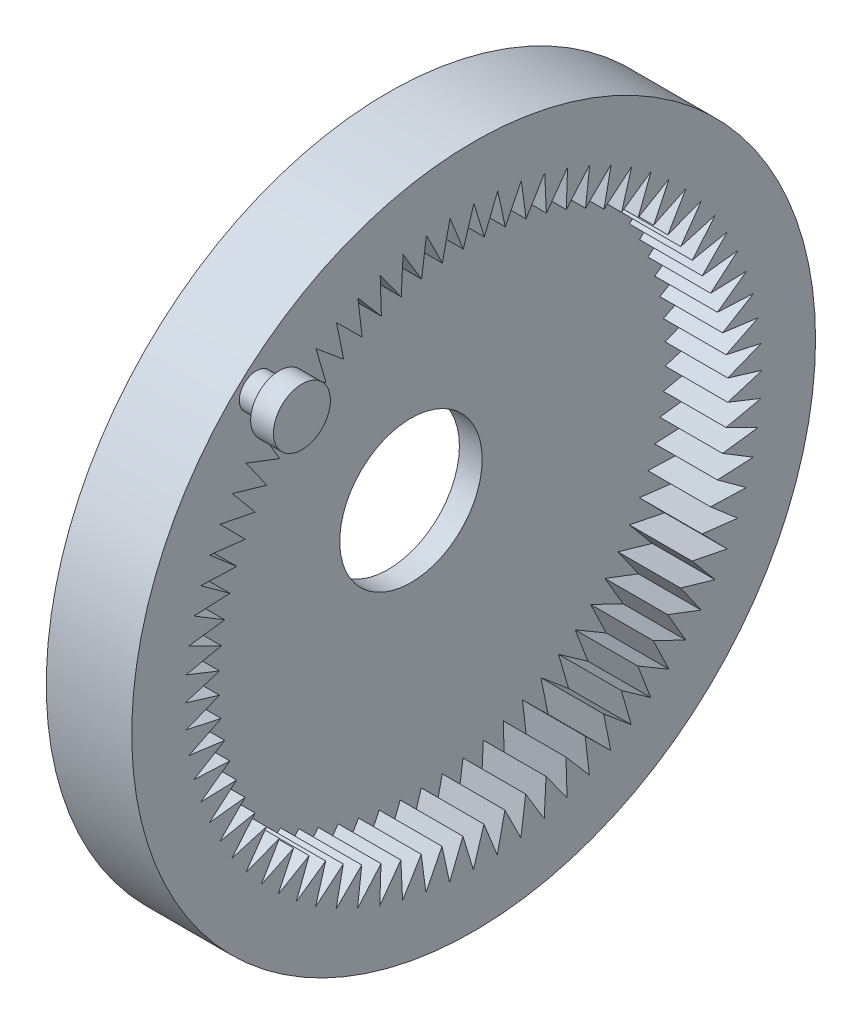
SolidWorks part; units mm, degrees
ref_plane "Front Plane" through (0, 0, 0) normal (0, 0, 1) x (1, 0, 0)
ref_plane "Top Plane" through (0, 0, 0) normal (0, 1, 0) x (1, 0, 0)
ref_plane "Right Plane" through (0, 0, 0) normal (1, 0, 0) x (0, 0, -1)
sketch "Sketch1" plane through (0, 0, 0) normal (1, 0, 0) x (0, 0, -1)
  circle A0 centre (0, 0) radius 30
  dimension "D1" = 60
extrude "Boss-Extrude1" add sketch "Sketch1" along normal blind 7.5
sketch "Sketch4" plane through (7.5, 0, 0) normal (1, 0, 0) x (0, -1, 0)
  line L0 (8.2003, -23.949) -> (8.0956, -20.7964)
  line L1 (8.2003, -23.949) -> (7.2077, -21.0502) construction
  line L2 (8.2003, -23.949) -> (6.3506, -21.3939)
  line L3 (6.1946, -24.5444) -> (6.3506, -21.3939)
  line L5 (6.1946, -24.5444) -> (4.5623, -21.8453)
  line L6 (4.1466, -24.9721) -> (4.5623, -21.8453)
  line L7 (4.1466, -24.9721) -> (2.7427, -22.1474)
  line L8 (2.0703, -25.2292) -> (2.7427, -22.1474)
  line L9 (2.0703, -25.2292) -> (0.9044, -22.2983)
  line L10 (-0.0202, -25.314) -> (0.9044, -22.2983)
  line L11 (-0.0202, -25.314) -> (-0.9401, -22.2968)
  line L12 (-2.1106, -25.2259) -> (-0.9401, -22.2968)
  line L13 (-2.1106, -25.2259) -> (-2.7781, -22.143)
  line L14 (-4.1865, -24.9654) -> (-2.7781, -22.143)
  line L15 (-4.1865, -24.9654) -> (-4.5972, -21.838)
  line L16 (-6.2338, -24.5345) -> (-4.5972, -21.838)
  line L17 (-6.2338, -24.5345) -> (-6.3848, -21.3837)
  line L18 (-8.2386, -23.9359) -> (-6.3848, -21.3837)
  line L19 (-8.2386, -23.9359) -> (-8.1289, -20.7835)
  line L20 (-10.1871, -23.1738) -> (-8.1289, -20.7835)
  line L21 (-10.1871, -23.1738) -> (-9.8174, -20.0412)
  line L22 (-12.0659, -22.2534) -> (-9.8174, -20.0412)
  line L23 (-12.0659, -22.2534) -> (-11.4389, -19.162)
  line L24 (-13.8624, -21.181) -> (-11.4389, -19.162)
  line L25 (-13.8624, -21.181) -> (-12.9822, -18.152)
  line L26 (-15.5642, -19.9639) -> (-12.9822, -18.152)
  line L27 (-15.5642, -19.9639) -> (-14.4368, -17.0179)
  line L28 (-17.1596, -18.6104) -> (-14.4368, -17.0179)
  line L29 (-17.1596, -18.6104) -> (-15.7928, -15.7676)
  line L30 (-18.6378, -17.1298) -> (-15.7928, -15.7676)
  line L31 (-18.6378, -17.1298) -> (-17.041, -14.4096)
  line L32 (-19.9887, -15.5322) -> (-17.041, -14.4096)
  line L33 (-19.9887, -15.5322) -> (-18.1727, -12.9531)
  line L34 (-21.2031, -13.8285) -> (-18.1727, -12.9531)
  line L35 (-21.2031, -13.8285) -> (-19.1803, -11.4082)
  line L36 (-22.2726, -12.0304) -> (-19.1803, -11.4082)
  line L37 (-22.2726, -12.0304) -> (-20.0569, -9.7854)
  line L38 (-23.19, -10.15) -> (-20.0569, -9.7854)
  line L39 (-23.19, -10.15) -> (-20.7964, -8.0956)
  line L40 (-23.949, -8.2003) -> (-20.7964, -8.0956)
  line L41 (-23.949, -8.2003) -> (-21.3939, -6.3506)
  line L42 (-24.5444, -6.1946) -> (-21.3939, -6.3506)
  line L43 (-24.5444, -6.1946) -> (-21.8453, -4.5623)
  line L44 (-24.9721, -4.1466) -> (-21.8453, -4.5623)
  line L45 (-24.9721, -4.1466) -> (-22.1474, -2.7427)
  line L46 (-25.2292, -2.0703) -> (-22.1474, -2.7427)
  line L47 (-25.2292, -2.0703) -> (-22.2983, -0.9044)
  line L48 (-25.314, 0.0202) -> (-22.2983, -0.9044)
  line L49 (-25.314, 0.0202) -> (-22.2968, 0.9401)
  line L50 (-25.2259, 2.1106) -> (-22.2968, 0.9401)
  line L51 (-25.2259, 2.1106) -> (-22.143, 2.7781)
  line L52 (-24.9654, 4.1865) -> (-22.143, 2.7781)
  line L53 (-24.9654, 4.1865) -> (-21.838, 4.5972)
  line L54 (-24.5345, 6.2338) -> (-21.838, 4.5972)
  line L55 (-24.5345, 6.2338) -> (-21.3837, 6.3848)
  line L56 (-23.9359, 8.2386) -> (-21.3837, 6.3848)
  line L57 (-23.9359, 8.2386) -> (-20.7835, 8.1289)
  line L58 (-23.1738, 10.1871) -> (-20.7835, 8.1289)
  line L59 (-23.1738, 10.1871) -> (-20.0412, 9.8174)
  line L60 (-22.2534, 12.0659) -> (-20.0412, 9.8174)
  line L61 (-22.2534, 12.0659) -> (-19.162, 11.4389)
  line L62 (-21.181, 13.8624) -> (-19.162, 11.4389)
  line L63 (-21.181, 13.8624) -> (-18.152, 12.9822)
  line L64 (-19.9639, 15.5642) -> (-18.152, 12.9822)
  line L65 (-19.9639, 15.5642) -> (-17.0179, 14.4368)
  line L66 (-18.6104, 17.1596) -> (-17.0179, 14.4368)
  line L67 (-18.6104, 17.1596) -> (-15.7676, 15.7928)
  line L68 (-17.1298, 18.6378) -> (-15.7676, 15.7928)
  line L69 (-17.1298, 18.6378) -> (-14.4096, 17.041)
  line L70 (-15.5322, 19.9887) -> (-14.4096, 17.041)
  line L71 (-15.5322, 19.9887) -> (-12.9531, 18.1727)
  line L72 (-13.8285, 21.2031) -> (-12.9531, 18.1727)
  line L73 (-13.8285, 21.2031) -> (-11.4082, 19.1803)
  line L74 (-12.0304, 22.2726) -> (-11.4082, 19.1803)
  line L75 (-12.0304, 22.2726) -> (-9.7854, 20.0569)
  line L76 (-10.15, 23.19) -> (-9.7854, 20.0569)
  line L77 (-10.15, 23.19) -> (-8.0956, 20.7964)
  line L78 (-8.2003, 23.949) -> (-8.0956, 20.7964)
  line L79 (-8.2003, 23.949) -> (-6.3506, 21.3939)
  line L80 (-6.1946, 24.5444) -> (-6.3506, 21.3939)
  line L81 (-6.1946, 24.5444) -> (-4.5623, 21.8453)
  line L82 (-4.1466, 24.9721) -> (-4.5623, 21.8453)
  line L83 (-4.1466, 24.9721) -> (-2.7427, 22.1474)
  line L84 (-2.0703, 25.2292) -> (-2.7427, 22.1474)
  line L85 (-2.0703, 25.2292) -> (-0.9044, 22.2983)
  line L86 (0.0202, 25.314) -> (-0.9044, 22.2983)
  line L87 (0.0202, 25.314) -> (0.9401, 22.2968)
  line L88 (2.1106, 25.2259) -> (0.9401, 22.2968)
  line L89 (2.1106, 25.2259) -> (2.7781, 22.143)
  line L90 (4.1865, 24.9654) -> (2.7781, 22.143)
  line L91 (4.1865, 24.9654) -> (4.5972, 21.838)
  line L92 (6.2338, 24.5345) -> (4.5972, 21.838)
  line L93 (6.2338, 24.5345) -> (6.3848, 21.3837)
  line L94 (8.2386, 23.9359) -> (6.3848, 21.3837)
  line L95 (8.2386, 23.9359) -> (8.1289, 20.7835)
  line L96 (10.1871, 23.1738) -> (8.1289, 20.7835)
  line L97 (10.1871, 23.1738) -> (9.8174, 20.0412)
  line L98 (12.0659, 22.2534) -> (9.8174, 20.0412)
  line L99 (12.0659, 22.2534) -> (11.4389, 19.162)
  line L100 (13.8624, 21.181) -> (11.4389, 19.162)
  line L101 (13.8624, 21.181) -> (12.9822, 18.152)
  line L102 (15.5642, 19.9639) -> (12.9822, 18.152)
  line L103 (15.5642, 19.9639) -> (14.4368, 17.0179)
  line L104 (17.1596, 18.6104) -> (14.4368, 17.0179)
  line L105 (17.1596, 18.6104) -> (15.7928, 15.7676)
  line L106 (18.6378, 17.1298) -> (15.7928, 15.7676)
  line L107 (18.6378, 17.1298) -> (17.041, 14.4096)
  line L108 (19.9887, 15.5322) -> (17.041, 14.4096)
  line L109 (19.9887, 15.5322) -> (18.1727, 12.9531)
  line L110 (21.2031, 13.8285) -> (18.1727, 12.9531)
  line L111 (21.2031, 13.8285) -> (19.1803, 11.4082)
  line L112 (22.2726, 12.0304) -> (19.1803, 11.4082)
  line L113 (22.2726, 12.0304) -> (20.0569, 9.7854)
  line L114 (23.19, 10.15) -> (20.0569, 9.7854)
  line L115 (23.19, 10.15) -> (20.7964, 8.0956)
  line L116 (23.949, 8.2003) -> (20.7964, 8.0956)
  line L117 (23.949, 8.2003) -> (21.3939, 6.3506)
  line L118 (24.5444, 6.1946) -> (21.3939, 6.3506)
  line L119 (24.5444, 6.1946) -> (21.8453, 4.5623)
  line L120 (24.9721, 4.1466) -> (21.8453, 4.5623)
  line L121 (24.9721, 4.1466) -> (22.1474, 2.7427)
  line L122 (25.2292, 2.0703) -> (22.1474, 2.7427)
  line L123 (25.2292, 2.0703) -> (22.2983, 0.9044)
  line L124 (25.314, -0.0202) -> (22.2983, 0.9044)
  line L125 (25.314, -0.0202) -> (22.2968, -0.9401)
  line L126 (25.2259, -2.1106) -> (22.2968, -0.9401)
  line L127 (25.2259, -2.1106) -> (22.143, -2.7781)
  line L128 (24.9654, -4.1865) -> (22.143, -2.7781)
  line L129 (24.9654, -4.1865) -> (21.838, -4.5972)
  line L130 (24.5345, -6.2338) -> (21.838, -4.5972)
  line L131 (24.5345, -6.2338) -> (21.3837, -6.3848)
  line L132 (23.9359, -8.2386) -> (21.3837, -6.3848)
  line L133 (23.9359, -8.2386) -> (20.7835, -8.1289)
  line L134 (23.1738, -10.1871) -> (20.7835, -8.1289)
  line L135 (23.1738, -10.1871) -> (20.0412, -9.8174)
  line L136 (22.2534, -12.0659) -> (20.0412, -9.8174)
  line L137 (22.2534, -12.0659) -> (19.162, -11.4389)
  line L138 (21.181, -13.8624) -> (19.162, -11.4389)
  line L139 (21.181, -13.8624) -> (18.152, -12.9822)
  line L140 (19.9639, -15.5642) -> (18.152, -12.9822)
  line L141 (19.9639, -15.5642) -> (17.0179, -14.4368)
  line L142 (18.6104, -17.1596) -> (17.0179, -14.4368)
  line L143 (18.6104, -17.1596) -> (15.7676, -15.7928)
  line L144 (17.1298, -18.6378) -> (15.7676, -15.7928)
  line L145 (17.1298, -18.6378) -> (14.4096, -17.041)
  line L146 (15.5322, -19.9887) -> (14.4096, -17.041)
  line L147 (15.5322, -19.9887) -> (12.9531, -18.1727)
  line L148 (13.8285, -21.2031) -> (12.9531, -18.1727)
  line L149 (13.8285, -21.2031) -> (11.4082, -19.1803)
  line L150 (12.0304, -22.2726) -> (11.4082, -19.1803)
  line L151 (12.0304, -22.2726) -> (9.7854, -20.0569)
  line L152 (10.15, -23.19) -> (9.7854, -20.0569)
  line L153 (10.15, -23.19) -> (8.0956, -20.7964)
  line L184 (7.2077, -21.0502) -> (8.5243, -24.8951) construction
  point P235 (0, 0)
  dimension "D1" = 17
extrude "Cut-Extrude2" cut sketch "Sketch4" against normal blind 5.5
sketch "Sketch6" plane through (2, 0, 0) normal (1, 0, 0) x (0, 0, -1)
  circle A0 centre (0, 0) radius 6.25
  dimension "D1" = 12.5
extrude "Cut-Extrude3" cut sketch "Sketch6" against normal through all
sketch "Sketch9" plane through (7.5, 0, 0) normal (1, 0, 0) x (0, 0, -1)
  circle A0 centre (-19.0657, 20.6344) radius 1.5
  dimension "D1" = 3
extrude "Boss-Extrude5" add sketch "Sketch9" along normal blind 2
sketch "Sketch10" plane through (9.5, 0, 0) normal (1, 0, 0) x (0, 0, -1)
  circle A0 centre (-19.0657, 20.6344) radius 2.5
  dimension "D1" = 5
extrude "Boss-Extrude6" add sketch "Sketch10" along normal blind 2
